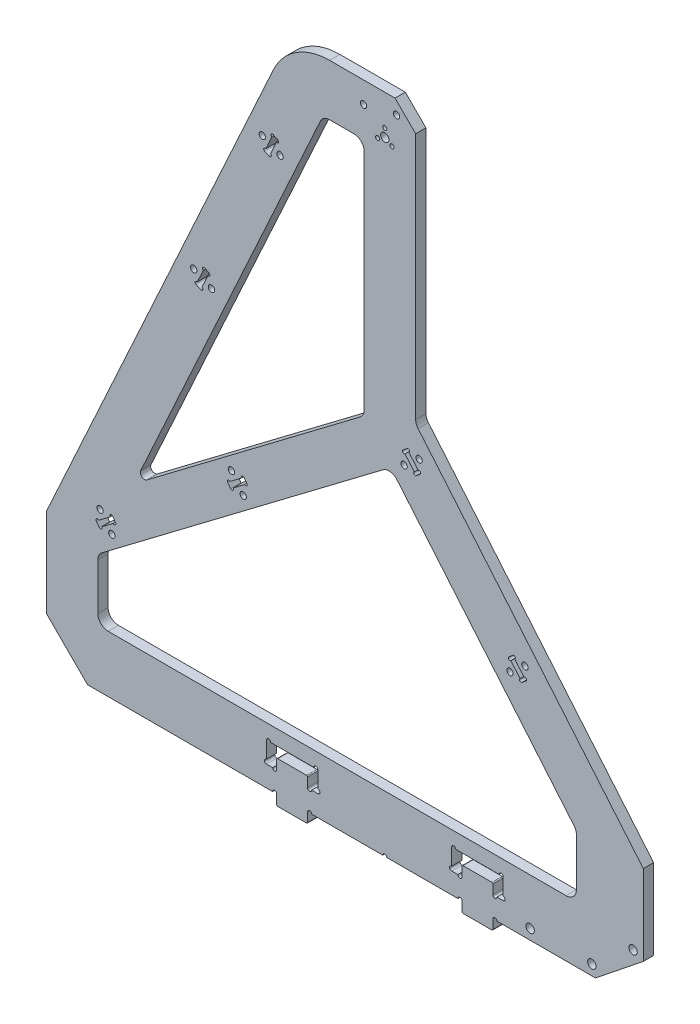
SolidWorks part; units mm, degrees
ref_plane "前视基准面" through (0, 0, 0) normal (0, 0, 1) x (1, 0, 0)
ref_plane "上视基准面" through (0, 0, 0) normal (0, 1, 0) x (1, 0, 0)
ref_plane "右视基准面" through (0, 0, 0) normal (1, 0, 0) x (0, 0, -1)
sketch "草图1" plane through (0, 0, 0) normal (0, 0, 1) x (1, 0, 0)
  line L10 (93.1, -245) -> (93.1, -275)
  line L11 (93.1, -275) -> (-139.4, -275)
  line L12 (-139.4, -275) -> (-139.4, -245)
  line L13 (-139.4, -245) -> (-30, -6)
  line L14 (-30, -6) -> (-10, -6)
  line L18 (-46.0511, 19) -> (15, 19)
  line L19 (-46.0511, 19) -> (-164.4, -239.5501)
  line L20 (-164.4, -239.5501) -> (-164.4, -302.5)
  line L21 (-164.4, -302.5) -> (125.6, -302.5)
  line L22 (125.6, -302.5) -> (125.6, -244.8389)
  line L24 (-10, -6) -> (-10, -122.1302)
  line L25 (-10, -122.1302) -> (93.1, -245)
  line L26 (15, 19) -> (15, -113.0309)
  line L27 (15, -113.0309) -> (125.6, -244.8389)
  circle A0 centre (0, 0) radius 2
  circle A1 centre (0, 0) radius 4 construction
  circle A2 centre (0, 4) radius 1
  circle A3 centre (3.4641, -2) radius 1
  circle A4 centre (-3.4641, -2) radius 1
  circle A5 centre (70.6, -297.5) radius 2.05
  circle A6 centre (100.6, -297.5) radius 2.05
  circle A7 centre (120.6, -281.5) radius 2.05
  point P13 (0, 0)
  dimension "D1" = 4
  dimension "D2" = 8
  dimension "D3" = 2
  dimension "D5" = 27.5
  dimension "D7" = 297.5
  dimension "D8" = 70.6
  dimension "D9" = 30
  dimension "D10" = 20
  dimension "D11" = 16
  dimension "D12" = 4.1
  dimension "D19" = 5
  dimension "D23" = 19
  dimension "D6" = 232.5
  dimension "D13" = 22.5
  dimension "D14" = 30
  dimension "D15" = 25
  dimension "D16" = 30
  dimension "D17" = 6
  dimension "D18" = 25
  dimension "D20" = 5
  dimension "D21" = 50
  dimension "D22" = 25
  dimension "D24" = 15
  dimension "D25" = 25
  dimension "D4" = 3
extrude "凸台-拉伸1" add sketch "草图1" along normal mid plane 5
sketch "草图2" plane through (0, 0, 2.5) normal (0, 0, 1) x (1, 0, 0)
  line L0 (-128.7102, -221.6466) -> (15, -113.0309) construction
  line L1 (-30, -6) -> (-139.4, -245) construction
  line L2 (-139.4, -245) -> (2.8724, -137.471)
  line L4 (-121.8546, -206.6695) -> (-10, -122.1302)
  line L5 (93.1, -245) -> (-10, -122.1302) construction
  line L6 (2.8724, -137.471) -> (-10, -122.1302)
  line L7 (-121.8546, -206.6695) -> (-139.4, -245)
  dimension "D1" = 20
extrude "凸台-拉伸2" add sketch "草图2" against normal blind 5
chamfer "倒角1" distance 10 angle 45 1 edges at (15, 19, 0)
fillet "圆角1" radius 5 9 edges at (2.8724, -137.471, 0) (-139.4, -275, 0) (93.1, -275, 0) (93.1, -245, 0) (-139.4, -245, 0) (-30, -6, 0) (-10, -6, 0) (-10, -122.1302, 0) (15, -113.0309, 0)
fillet "圆角2" radius 2 1 edges at (-121.8546, -206.6695, 0)
chamfer "倒角2" distance 20 angle 45 1 edges at (-164.4, -302.5, 0)
fillet "圆角3" radius 30 1 edges at (-46.0511, 19, 0)
sketch "草图3" plane through (0, 0, 2.5) normal (0, 0, 1) x (1, 0, 0)
  line L0 (125.6, -283.9031) -> (102.3539, -302.5)
  line L1 (125.6, -302.5) -> (125.6, -244.8389) construction
  line L2 (102.3539, -302.5) -> (125.6, -302.5)
  line L3 (125.6, -302.5) -> (125.6, -283.9031)
  line L4 (-144.4, -302.5) -> (125.6, -302.5) construction
  circle A0 centre (120.6, -281.5) radius 2.05 construction
  circle A1 centre (100.6, -297.5) radius 2.05 construction
  dimension "D2" = 5
  dimension "D1" = 5
extrude "切除-拉伸1" cut sketch "草图3" against normal through all
sketch "草图4" plane through (0, 0, 2.5) normal (0, 0, 1) x (1, 0, 0)
  line L0 (10.7818, -125.5058) -> (8.8667, -127.1127)
  line L1 (8.8667, -127.1127) -> (15.2624, -134.7349)
  line L2 (15.2624, -134.7349) -> (17.1775, -133.1279)
  line L3 (17.1775, -133.1279) -> (10.7818, -125.5058)
  line L4 (48.3092, -152.7273) -> (29.158, -168.7969) construction
  line L5 (125.6, -244.8389) -> (16.1698, -114.425) construction
  line L6 (91.9302, -243.6059) -> (5.9267, -141.1109) construction
  line L7 (16.22, -133.9314) -> (38.7336, -160.7621) construction
  line L8 (60.2897, -188.3963) -> (62.2048, -186.7893)
  line L9 (66.6854, -196.0184) -> (60.2897, -188.3963)
  line L10 (68.6005, -194.4115) -> (66.6854, -196.0184)
  line L11 (62.2048, -186.7893) -> (68.6005, -194.4115)
  line L12 (-138.6818, -233.4892) -> (-130.744, -227.4898)
  line L13 (-130.744, -227.4898) -> (-132.2513, -225.4954)
  line L14 (-132.2513, -225.4954) -> (-140.1892, -231.4948)
  line L15 (-140.1892, -231.4948) -> (-138.6818, -233.4892)
  line L16 (-137.4148, -243.4996) -> (-0.9183, -140.336) construction
  line L17 (-109.5851, -197.3963) -> (-97.526, -213.3518) construction
  line L18 (-11.9852, -123.6306) -> (-115.5311, -201.8902) construction
  line L19 (-131.4977, -226.4926) -> (-103.5556, -205.3741) construction
  line L20 (-76.3672, -183.2583) -> (-68.4294, -177.2589)
  line L21 (-74.8598, -185.2528) -> (-76.3672, -183.2583)
  line L22 (-66.922, -179.2534) -> (-74.8598, -185.2528)
  line L23 (-68.4294, -177.2589) -> (-66.922, -179.2534)
  line L24 (0, 0) -> (-32.0669, 14.953) construction
  line L25 (-22.558, 35.345) -> (-41.5758, -5.4389) construction
  line L26 (-15, -6) -> (-26.7898, -6) construction
  line L28 (-54.2542, -25.9505) -> (-51.981, -26.9911)
  line L29 (-51.981, -26.9911) -> (-56.1223, -36.0383)
  line L30 (-56.1223, -36.0383) -> (-58.3955, -34.9978)
  line L31 (-58.3955, -34.9978) -> (-54.2542, -25.9505)
  line L32 (-31.3361, -8.919) -> (-118.5555, -199.4623) construction
  line L33 (-83.2025, -62.1625) -> (-60.4708, -72.5678) construction
  line L34 (-54.0678, 1.4863) -> (-164.4, -239.5501) construction
  line L35 (-57.2589, -35.518) -> (-71.8366, -67.3652) construction
  line L36 (-85.2778, -99.7326) -> (-87.5509, -98.692)
  line L37 (-89.4191, -108.7798) -> (-85.2778, -99.7326)
  line L38 (-91.6922, -107.7393) -> (-89.4191, -108.7798)
  line L39 (-87.5509, -98.692) -> (-91.6922, -107.7393)
  line L40 (-92.804, -101.7589) -> (-84.166, -105.7129) construction
  line L41 (-74.5086, -177.4664) -> (-68.7806, -185.0453) construction
  line L42 (60.8064, -194.4571) -> (68.0838, -188.3506) construction
  arc A0 (15, -111.2111) -> (16.1698, -114.425) centre (20, -111.2111) ccw construction
  arc A1 (-137.4148, -243.4996) -> (-139.4, -247.4884) centre (-134.4, -247.4884) ccw construction
  arc A3 (-26.7898, -6) -> (-31.3361, -8.919) centre (-26.7898, -11) ccw construction
  circle A4 centre (-84.166, -105.7129) radius 1.55
  circle A5 centre (-92.804, -101.7589) radius 1.55
  circle A6 centre (-50.8692, -32.9714) radius 1.55
  circle A7 centre (-59.5073, -29.0174) radius 1.55
  circle A8 centre (-74.5086, -177.4664) radius 1.55
  circle A9 centre (-68.7806, -185.0453) radius 1.55
  circle A10 centre (-132.6025, -233.2817) radius 1.55
  circle A11 centre (-138.3306, -225.7028) radius 1.55
  circle A12 centre (68.0838, -188.3506) radius 1.55
  circle A13 centre (60.8064, -194.4571) radius 1.55
  circle A14 centre (16.6608, -127.0671) radius 1.55
  circle A15 centre (9.3834, -133.1736) radius 1.55
  point P10 (13.9797, -129.3168)
  point P32 (-136.2203, -228.4951)
  point P47 (-32.0669, 14.953)
  point P62 (-56.3248, -30.4741)
  point P73 (-88.485, -103.7359)
  point P74 (-89.6216, -103.2157)
  point P83 (-72.3983, -180.2586)
  point P84 (-71.6446, -181.2558)
  point P91 (65.4027, -190.6004)
  point P92 (64.4451, -191.4039)
  dimension "D6" = 50
  dimension "D7" = 45
  dimension "D11" = 3.5
  dimension "D12" = 3.1
  dimension "D13" = 3.5
  dimension "D14" = 3.1
  dimension "D15" = 3.5
  dimension "D1" = 9.95
  dimension "D2" = 2.5
  dimension "D3" = 80
  dimension "D4" = 50
  dimension "D5" = 80
  dimension "D8" = 25
  dimension "D9" = 80
  dimension "D10" = 70
extrude "切除-拉伸2" cut sketch "草图4" against normal through all
sketch "草图5" plane through (0, 0, 2.5) normal (0, 0, 1) x (1, 0, 0)
  line L0 (-89.4191, -108.7798) -> (-85.2778, -99.7326) construction
  line L1 (-87.5509, -98.692) -> (-91.6922, -107.7393) construction
  line L2 (-54.2542, -25.9505) -> (-58.3955, -34.9978) construction
  line L3 (-56.1223, -36.0383) -> (-51.981, -26.9911) construction
  line L4 (-132.2513, -225.4954) -> (-140.1892, -231.4948) construction
  line L5 (-138.6818, -233.4892) -> (-130.744, -227.4898) construction
  line L6 (-74.8598, -185.2528) -> (-66.922, -179.2534) construction
  line L7 (-68.4294, -177.2589) -> (-76.3672, -183.2583) construction
  line L8 (8.8667, -127.1127) -> (15.2624, -134.7349) construction
  line L9 (17.1775, -133.1279) -> (10.7818, -125.5058) construction
  line L10 (60.2897, -188.3963) -> (66.6854, -196.0184) construction
  line L11 (68.6005, -194.4115) -> (62.2048, -186.7893) construction
  circle A0 centre (-85.5899, -100.4145) radius 0.75
  circle A1 centre (-87.8631, -99.374) radius 0.75
  circle A2 centre (-91.3801, -107.0573) radius 0.75
  circle A3 centre (-89.1069, -108.0978) radius 0.75
  circle A4 centre (-58.0833, -34.3158) radius 0.75
  circle A5 centre (-55.8102, -35.3563) radius 0.75
  circle A6 centre (-54.5664, -26.6325) radius 0.75
  circle A7 centre (-52.2932, -27.673) radius 0.75
  circle A8 centre (-139.5909, -231.0425) radius 0.75
  circle A9 centre (-138.0835, -233.037) radius 0.75
  circle A10 centre (-132.8497, -225.9476) radius 0.75
  circle A11 centre (-131.3423, -227.942) radius 0.75
  circle A12 centre (-74.2615, -184.8005) radius 0.75
  circle A13 centre (-75.7689, -182.8061) radius 0.75
  circle A14 centre (-69.0277, -177.7111) radius 0.75
  circle A15 centre (-67.5203, -179.7056) radius 0.75
  circle A16 centre (9.3488, -127.6873) radius 0.75
  circle A17 centre (11.2639, -126.0803) radius 0.75
  circle A18 centre (14.7803, -134.1603) radius 0.75
  circle A19 centre (16.6954, -132.5534) radius 0.75
  circle A20 centre (60.7718, -188.9708) radius 0.75
  circle A21 centre (62.6869, -187.3639) radius 0.75
  circle A22 centre (66.2033, -195.4439) radius 0.75
  circle A23 centre (68.1184, -193.8369) radius 0.75
  dimension "D1" = 1.5
extrude "切除-拉伸3" cut sketch "草图5" against normal through all
sketch "草图6" plane through (0, 0, 2.5) normal (0, 0, 1) x (1, 0, 0)
  line L0 (-10.3416, 8.6776) -> (0, 0) construction
  line L1 (0, 0) -> (5.7053, 12.2352) construction
  line L2 (-1.1766, 13.4486) -> (0, 0) construction
  line L3 (0, 0) -> (-4.6173, 12.6859) construction
  line L4 (0, 0) -> (0, 13.5) construction
  circle A0 centre (0, 0) radius 13.5 construction
  circle A2 centre (-10.3416, 8.6776) radius 1.55
  circle A3 centre (5.7053, 12.2352) radius 1.55
  dimension "D1" = 27
  dimension "D2" = 3.1
  dimension "D3" = 15
  dimension "D4" = 30
  dimension "D5" = 30
  dimension "D6" = 5
extrude "切除-拉伸4" cut sketch "草图6" against normal through all
sketch "草图7" plane through (0, 0, 2.5) normal (0, 0, 1) x (1, 0, 0)
  line L0 (-144.4, -302.5) -> (102.3539, -302.5) construction
  circle A0 centre (0, -302.5) radius 1
  dimension "D1" = 2
extrude "切除-拉伸5" cut sketch "草图7" against normal through all
sketch "草图8" plane through (0, 0, 2.5) normal (0, 0, 1) x (1, 0, 0)
  line L5 (-144.4, -302.5) -> (-1, -302.5) construction
  line L6 (-37.5, -307.5) -> (-52.5, -307.5)
  line L7 (-37.5, -307.5) -> (-37.5, -302.5)
  line L8 (-37.5, -302.5) -> (-52.5, -302.5)
  line L9 (-52.5, -307.5) -> (-52.5, -302.5)
  line L10 (-37.5, -307.5) -> (-52.5, -302.5) construction
  line L11 (-37.5, -302.5) -> (-52.5, -307.5) construction
  line L12 (0, -302.5) -> (0, -275) construction
  line L13 (-134.4, -275) -> (88.1, -275) construction
  line L14 (37.5, -302.5) -> (52.5, -302.5)
  line L15 (52.5, -307.5) -> (52.5, -302.5)
  line L16 (37.5, -307.5) -> (52.5, -307.5)
  line L17 (37.5, -307.5) -> (37.5, -302.5)
  point P0 (-45, -305)
  dimension "D1" = 90
  dimension "D2" = 15
  dimension "D3" = 5
extrude "凸台-拉伸3" add sketch "草图8" against normal blind 5
sketch "草图10" plane through (0, 0, 2.5) normal (0, 0, 1) x (1, 0, 0)
  line L0 (-57.5, -282.3) -> (-57.5, -292.4)
  line L1 (-57.5, -292.4) -> (-52.5, -292.4)
  line L2 (-52.5, -292.4) -> (-52.5, -287.4)
  line L3 (-52.5, -287.4) -> (-37.5, -287.4)
  line L4 (-37.5, -287.4) -> (-37.5, -292.4)
  line L5 (-37.5, -292.4) -> (-32.5, -292.4)
  line L6 (-32.5, -292.4) -> (-32.5, -282.3)
  line L7 (-32.5, -282.3) -> (-57.5, -282.3)
  line L8 (0, -301.5) -> (0, -275) construction
  line L9 (-134.4, -275) -> (88.1, -275) construction
  line L10 (-52.5, -302.5) -> (-52.5, -307.5) construction
  line L11 (-37.5, -307.5) -> (-37.5, -302.5) construction
  line L12 (-144.4, -302.5) -> (-52.5, -302.5) construction
  line L13 (32.5, -282.3) -> (57.5, -282.3)
  line L14 (32.5, -292.4) -> (32.5, -282.3)
  line L15 (37.5, -292.4) -> (32.5, -292.4)
  line L16 (37.5, -287.4) -> (37.5, -292.4)
  line L17 (52.5, -287.4) -> (37.5, -287.4)
  line L18 (52.5, -292.4) -> (52.5, -287.4)
  line L19 (57.5, -292.4) -> (52.5, -292.4)
  line L20 (57.5, -282.3) -> (57.5, -292.4)
  arc A0 (1, -302.5) -> (-1, -302.5) centre (0, -302.5) ccw construction
  dimension "D1" = 5
  dimension "D2" = 5.1
  dimension "D3" = 25
  dimension "D4" = 10.1
extrude "切除-拉伸7" cut sketch "草图10" against normal through all
sketch "草图9" plane through (0, 0, 2.5) normal (0, 0, 1) x (1, 0, 0)
  line L0 (-144.4, -302.5) -> (-52.5, -302.5) construction
  line L1 (-37.5, -302.5) -> (-1, -302.5) construction
  line L2 (1, -302.5) -> (37.5, -302.5) construction
  line L3 (52.5, -302.5) -> (102.3539, -302.5) construction
  line L4 (-57.5, -292.4) -> (-52.5, -292.4) construction
  line L5 (-57.5, -282.3) -> (-57.5, -292.4) construction
  line L6 (-32.5, -292.4) -> (-32.5, -282.3) construction
  line L7 (-37.5, -292.4) -> (-32.5, -292.4) construction
  line L8 (-32.5, -282.3) -> (-57.5, -282.3) construction
  line L9 (0, -301.5) -> (0, -275) construction
  line L10 (-134.4, -275) -> (88.1, -275) construction
  circle A0 centre (-53.5, -302.5) radius 1
  circle A1 centre (-36.5, -302.5) radius 1
  circle A2 centre (36.5, -302.5) radius 1
  circle A3 centre (53.5, -302.5) radius 1
  arc A4 (1, -302.5) -> (-1, -302.5) centre (0, -302.5) ccw construction
  circle A5 centre (-53.5, -292.4) radius 1
  circle A6 centre (-57.5, -291.4) radius 1
  circle A7 centre (-32.5, -291.4) radius 1
  circle A8 centre (-36.5, -292.4) radius 1
  circle A9 centre (-33.5, -282.3) radius 1
  circle A10 centre (-56.5, -282.3) radius 1
  circle A11 centre (56.5, -282.3) radius 1
  circle A12 centre (57.5, -291.4) radius 1
  circle A13 centre (53.5, -292.4) radius 1
  circle A14 centre (36.5, -292.4) radius 1
  circle A15 centre (32.5, -291.4) radius 1
  circle A16 centre (33.5, -282.3) radius 1
extrude "切除-拉伸6" cut sketch "草图9" against normal through all
fillet "圆角4" radius 0.5 8 edges at (52.5, -307.5, 0) (37.5, -307.5, 0) (-37.5, -307.5, 0) (-52.5, -307.5, 0) (52.5, -287.4, 0) (37.5, -287.4, 0) (-37.5, -287.4, 0) (-52.5, -287.4, 0)
